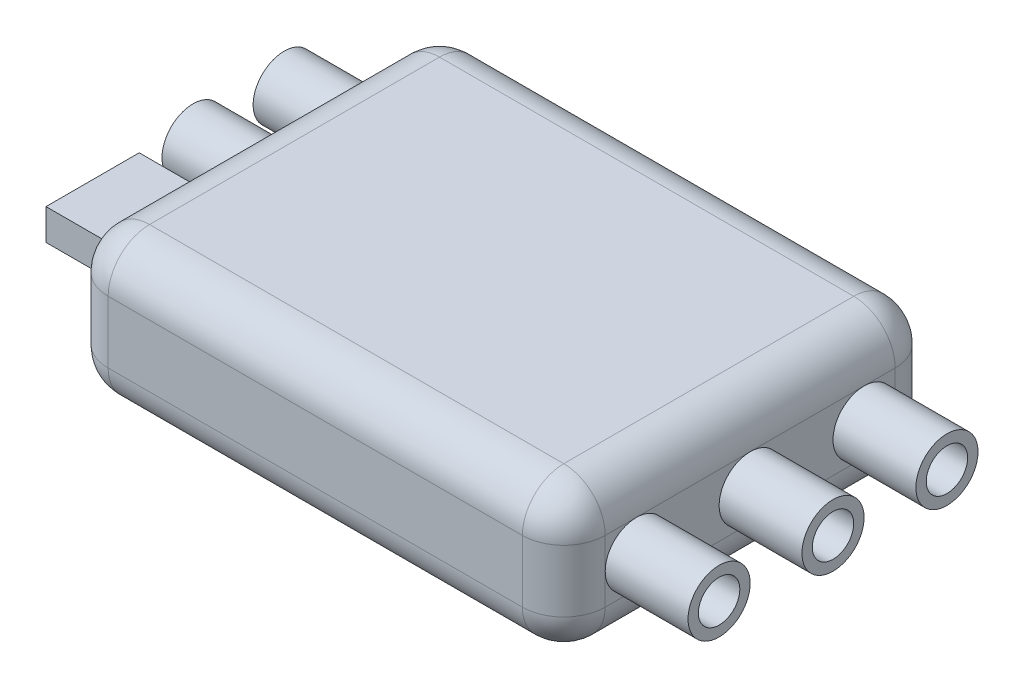
SolidWorks part; units mm, degrees
ref_plane "Front Plane" through (0, 0, 0) normal (0, 0, 1) x (1, 0, 0)
ref_plane "Top Plane" through (0, 0, 0) normal (0, 1, 0) x (1, 0, 0)
ref_plane "Right Plane" through (0, 0, 0) normal (1, 0, 0) x (0, 0, -1)
sketch "Sketch1" plane through (0, 0, 0) normal (0, 1, 0) x (1, 0, 0)
  line L1 (-12, -9) -> (12, -9)
  line L2 (-12, -9) -> (-12, 9)
  line L3 (-12, 9) -> (12, 9)
  line L4 (12, -9) -> (12, 9)
  line L5 (-12, -9) -> (12, 9) construction
  line L6 (-12, 9) -> (12, -9) construction
  point P0 (0, 0)
  dimension "D1" = 18
  dimension "D2" = 24
extrude "Boss-Extrude1" add sketch "Sketch1" along normal blind 7
fillet "Fillet2" radius 2 12 edges at (-12, 3.5, -9) (-12, 3.5, 9) (0, 0, -9) (-12, 0, 0) (0, 0, 9) (12, 3.5, 9) (12, 3.5, -9) (12, 0, 0) (0, 7, 9) (-12, 7, 0) (0, 7, -9) (12, 7, 0)
sketch "Sketch2" plane through (12, 0, 0) normal (1, 0, 0) x (0, 0, -1)
  line L0 (-7, 3.5) -> (7, 3.5) construction
  line L1 (-7, 5) -> (-7, 2) construction
  line L2 (7, 2) -> (7, 5) construction
  circle A0 centre (-5.5, 3.5) radius 1.5
  circle A1 centre (-5.5, 3.5) radius 1
  circle A2 centre (0, 3.5) radius 1.5
  circle A3 centre (0, 3.5) radius 1
  circle A4 centre (5.5, 3.5) radius 1.5
  circle A5 centre (5.5, 3.5) radius 1
  dimension "D1" = 3
  dimension "D2" = 2
  dimension "D3" = 3
extrude "Boss-Extrude2" add sketch "Sketch2" along normal blind 4
sketch "Sketch3" plane through (-12, 0, 0) normal (-1, 0, 0) x (0, 0, 1)
  line L0 (-7, 3.5) -> (7, 3.5) construction
  line L1 (-7, 5) -> (-7, 2) construction
  line L2 (7, 2) -> (7, 5) construction
  line L3 (7, 5) -> (-7, 5) construction
  line L5 (1.5, 2.75) -> (6, 2.75)
  line L6 (1.5, 2.75) -> (1.5, 4.25)
  line L7 (1.5, 4.25) -> (6, 4.25)
  line L8 (6, 2.75) -> (6, 4.25)
  line L9 (1.5, 2.75) -> (6, 4.25) construction
  line L10 (1.5, 4.25) -> (6, 2.75) construction
  circle A0 centre (-5.5, 3.5) radius 1.5
  circle A1 centre (-5.5, 3.5) radius 1
  circle A2 centre (-1.1, 3.5) radius 1.5
  circle A3 centre (-1.1, 3.5) radius 1
  point P11 (3.75, 3.5)
  dimension "D1" = 2
  dimension "D3" = 1.5
  dimension "D4" = 4.5
  dimension "D5" = 1
  dimension "D2" = 2
extrude "Boss-Extrude3" add sketch "Sketch3" along normal blind 4
